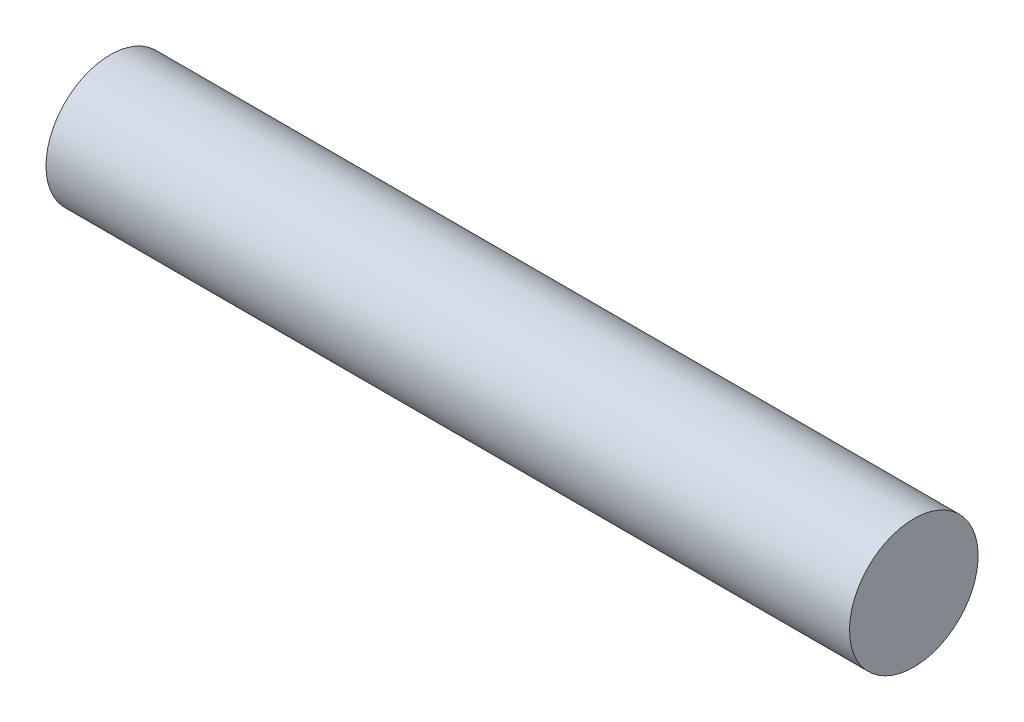
SolidWorks part; units mm, degrees
ref_plane "Plan de face" through (0, 0, 0) normal (0, 0, 1) x (1, 0, 0)
ref_plane "Plan de dessus" through (0, 0, 0) normal (0, 1, 0) x (1, 0, 0)
ref_plane "Plan de droite" through (0, 0, 0) normal (1, 0, 0) x (0, 0, -1)
sketch "Esquisse1" plane through (0, 0, 0) normal (0, 0, 1) x (1, 0, 0)
  line L0 (0, 4) -> (0, 3)
  line L1 (0, 4) -> (50, 4)
  line L2 (0, 3) -> (20, 3)
  line L3 (20, 3) -> (20, 0)
  line L4 (50, 4) -> (50, 0)
  line L8 (20, 0) -> (50, 0)
revolve "Révolution1" add sketch "Esquisse1" angle 360 about L8
